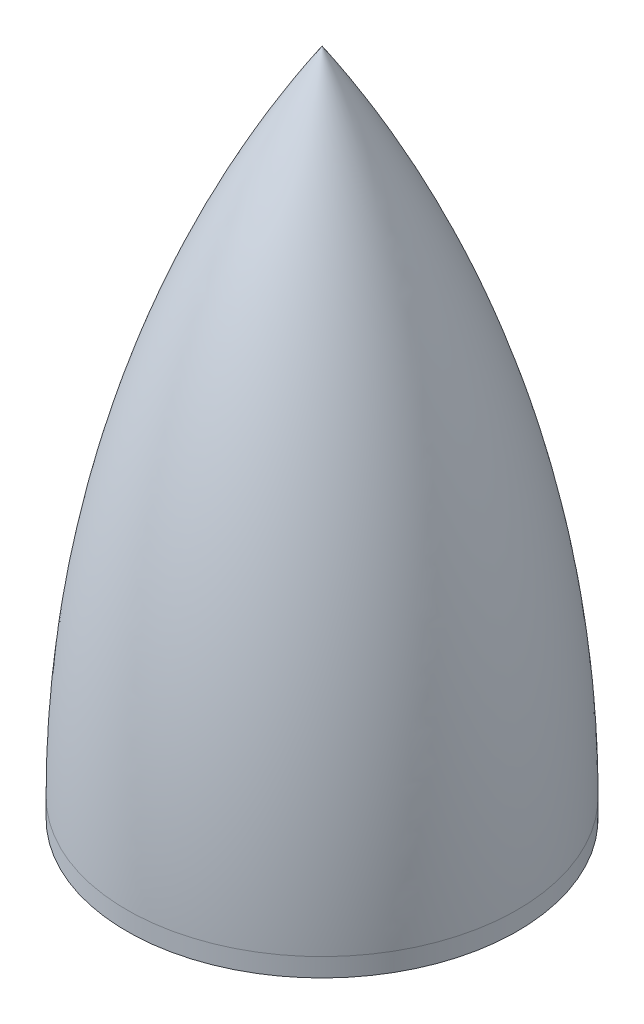
SolidWorks part; units mm, degrees
ref_plane "Front Plane" through (0, 0, 0) normal (0, 0, 1) x (1, 0, 0)
ref_plane "Top Plane" through (0, 0, 0) normal (0, 1, 0) x (1, 0, 0)
ref_plane "Right Plane" through (0, 0, 0) normal (1, 0, 0) x (0, 0, -1)
sketch "Sketch1" plane through (0, 0, 0) normal (0, 0, 1) x (1, 0, 0)
  line L0 (0, 0) -> (0, 65.3751) construction
  line L1 (-1.5875, 0) -> (-22.225, 0)
  line L2 (-22.225, 0) -> (-22.225, 2.1082)
  line L3 (-1.5875, 2.1082) -> (-1.5875, 6.35)
  line L4 (-1.5875, 0) -> (-1.5875, 2.1082)
  line L5 (-6.35, 2.1082) -> (-21.1836, 2.1082)
  line L6 (0, 76.2) -> (0, 73.8451)
  line L10 (-1.5875, 6.35) -> (-6.35, 6.35)
  line L11 (-6.35, 6.35) -> (-6.35, 2.1082)
  arc A0 (-22.225, 2.1082) -> (0, 76.2) centre (112.3879, 2.1082) cw
  arc A1 (-21.1836, 2.1082) -> (0, 73.8451) centre (113.4272, 1.3544) cw
  dimension "D1" = 1.0414
  dimension "D2" = 3.175
  dimension "D3" = 76.2
  dimension "D4" = 2.1082
  dimension "D5" = 6.35
  dimension "D6" = 44.45
  dimension "D7" = 12.7
revolve "Revolve1" add sketch "Sketch1" angle 360 mid plane about L0
